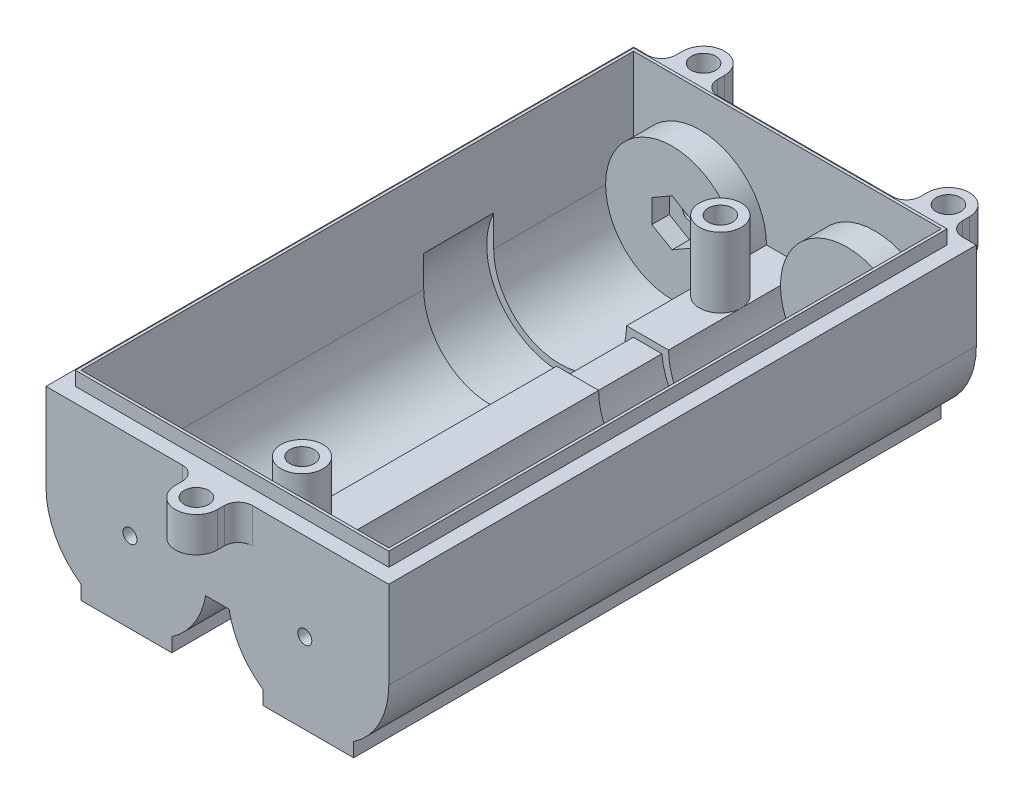
SolidWorks part; units mm, degrees
ref_plane "Спереди" through (0, 0, 0) normal (0, 0, 1) x (1, 0, 0)
ref_plane "Сверху" through (0, 0, 0) normal (0, 1, 0) x (1, 0, 0)
ref_plane "Справа" through (0, 0, 0) normal (1, 0, 0) x (0, 0, -1)
sketch "Эскиз1" plane through (0, 0, 0) normal (0, 1, 0) x (1, 0, 0)
  line L0 (-3, -45) -> (-3, -44)
  line L1 (22.5, 40) -> (-22.5, 40) construction
  line L2 (22.5, 40) -> (22.5, -40) construction
  line L3 (22.5, -40) -> (-22.5, -40) construction
  line L4 (-22.5, 40) -> (-22.5, -40) construction
  line L5 (22.5, 40) -> (-22.5, -40) construction
  line L6 (22.5, -40) -> (-22.5, 40) construction
  line L7 (22, -39.5) -> (-22, -39.5)
  line L8 (22, -39.5) -> (22, 39.5)
  line L9 (22, 39.5) -> (-22, 39.5)
  line L10 (-22, -39.5) -> (-22, 39.5)
  line L11 (22, -39.5) -> (-22, 39.5) construction
  line L12 (22, 39.5) -> (-22, -39.5) construction
  line L13 (24.5, -42) -> (5, -42)
  line L14 (24.5, -42) -> (24.5, 42)
  line L15 (24.5, 42) -> (22.5, 42)
  line L16 (-24.5, -42) -> (-24.5, 42)
  line L17 (24.5, -42) -> (-24.5, 42) construction
  line L18 (24.5, 42) -> (-24.5, -42) construction
  line L19 (-20.5, 45) -> (-20.5, 44)
  line L20 (3, -44) -> (3, -45)
  line L21 (-5, -42) -> (-24.5, -42)
  line L22 (-14.5, 45) -> (-14.5, 44)
  line L23 (14.5, 45) -> (14.5, 44)
  line L24 (20.5, 45) -> (20.5, 44)
  line L25 (12.5, 42) -> (-12.5, 42)
  line L26 (-22.5, 42) -> (-24.5, 42)
  circle A0 centre (-17.5, 45) radius 1.75
  circle A1 centre (17.5, 45) radius 1.75
  circle A2 centre (0, -45) radius 1.75
  arc A3 (-3, -45) -> (3, -45) centre (0, -45) ccw
  arc A4 (-14.5, 45) -> (-20.5, 45) centre (-17.5, 45) ccw
  arc A5 (20.5, 45) -> (14.5, 45) centre (17.5, 45) ccw
  arc A6 (5, -42) -> (3, -44) centre (5, -44) ccw
  arc A7 (-3, -44) -> (-5, -42) centre (-5, -44) ccw
  arc A8 (20.5, 44) -> (22.5, 42) centre (22.5, 44) ccw
  arc A9 (14.5, 44) -> (12.5, 42) centre (12.5, 44) cw
  arc A10 (-14.5, 44) -> (-12.5, 42) centre (-12.5, 44) ccw
  arc A11 (-20.5, 44) -> (-22.5, 42) centre (-22.5, 44) cw
  point P0 (0, 0)
  point P12 (0, -40)
  point P13 (0, 0)
  point P18 (0, 39.5)
  point P19 (-22, 0)
  point P20 (-22.5, 0)
  point P21 (0, 0)
  point P26 (-24.5, 0)
  point P27 (22, 0)
  point P44 (-3, -42)
  point P49 (14.5, 42)
  point P52 (-14.5, 42)
  point P55 (-20.5, 42)
  dimension "D3" = 3.5
  dimension "D4" = 3.5
  dimension "D5" = 5
  dimension "D9" = 3.5
  dimension "D16" = 6
  dimension "D17" = 6
  dimension "D18" = 6
  dimension "D19" = 2
  dimension "D1" = 45
  dimension "D2" = 80
  dimension "D6" = 5
  dimension "D7" = 5
  dimension "D8" = 5
  dimension "D10" = 5
  dimension "D11" = 0.5
  dimension "D12" = 0.5
  dimension "D13" = 2.5
  dimension "D14" = 2.5
  dimension "D15" = 2.5
extrude "Бобышка-Вытянуть1" add sketch "Эскиз1" along normal blind 5
sketch "Эскиз2" plane through (0, 0, 0) normal (0, -1, 0) x (1, 0, 0)
  line L1 (22, -39.5) -> (-22, -39.5)
  line L2 (22, -39.5) -> (22, 39.5)
  line L3 (22, 39.5) -> (-22, 39.5)
  line L4 (-22, -39.5) -> (-22, 39.5)
  line L5 (22, -39.5) -> (-22, 39.5) construction
  line L6 (22, 39.5) -> (-22, -39.5) construction
  line L7 (24.5, -42) -> (-24.5, -42)
  line L8 (24.5, -42) -> (24.5, 42)
  line L9 (24.5, 42) -> (-24.5, 42)
  line L10 (-24.5, -42) -> (-24.5, 42)
  line L11 (24.5, -42) -> (-24.5, 42) construction
  line L12 (24.5, 42) -> (-24.5, -42) construction
  point P0 (0, 0)
  point P7 (0, 0)
extrude "Бобышка-Вытянуть2" add sketch "Эскиз2" along normal blind 17
sketch "Эскиз3" plane through (0, 5, 0) normal (0, 1, 0) x (1, 0, 0)
  line L1 (22, -39.5) -> (-22, -39.5)
  line L2 (22, -39.5) -> (22, 39.5)
  line L3 (22, 39.5) -> (-22, 39.5)
  line L4 (-22, -39.5) -> (-22, 39.5)
  line L5 (22, -39.5) -> (-22, 39.5) construction
  line L6 (22, 39.5) -> (-22, -39.5) construction
  line L7 (-22.4, -39.9) -> (22.4, -39.9)
  line L8 (-22.4, -39.9) -> (-22.4, 39.9)
  line L9 (-22.4, 39.9) -> (22.4, 39.9)
  line L10 (22.4, -39.9) -> (22.4, 39.9)
  line L11 (-22.4, -39.9) -> (22.4, 39.9) construction
  line L12 (-22.4, 39.9) -> (22.4, -39.9) construction
  point P0 (0, 0)
  point P7 (0, 0)
  point P12 (0, 39.5)
  point P13 (0, 39.9)
  point P14 (22, 0)
  dimension "D1" = 0.4
  dimension "D2" = 0.4
extrude "Бобышка-Вытянуть3" add sketch "Эскиз3" along normal blind 2
sketch "Эскиз4" plane through (0, -17, 0) normal (0, -1, 0) x (1, 0, 0)
  line L1 (24.5, -42) -> (-24.5, -42)
  line L2 (24.5, -42) -> (24.5, 42)
  line L3 (24.5, 42) -> (-24.5, 42)
  line L4 (-24.5, -42) -> (-24.5, 42)
  line L5 (24.5, -42) -> (-24.5, 42) construction
  line L6 (24.5, 42) -> (-24.5, -42) construction
  point P0 (0, 0)
extrude "Бобышка-Вытянуть4" add sketch "Эскиз4" along normal blind 2
sketch "Эскиз5" plane through (0, 0, -39.5) normal (0, 0, 1) x (1, 0, 0)
  line L0 (-22, 7) -> (-22, -17) construction
  line L1 (-22, -17) -> (22, -17) construction
  line L2 (22, 7) -> (22, -17) construction
  line L3 (-3, -7.5) -> (3, -7.5)
  line L4 (-22, -7.5) -> (-22, -17)
  line L5 (-22, -17) -> (22, -17)
  line L6 (22, -17) -> (22, -7.5)
  arc A0 (-22, -7.5) -> (-3, -7.5) centre (-12.5, -7.5) ccw
  arc A1 (3, -7.5) -> (22, -7.5) centre (12.5, -7.5) ccw
  line M1 (-22, 7) -> (-22, -17)
  line M2 (-22, -17) -> (22, -17)
  line M3 (22, -17) -> (22, 7)
  dimension "D1" = 19
  dimension "D2" = 19
extrude "Бобышка-Вытянуть5" add sketch "Эскиз5" along normal up to surface (79 mm away) contours A1 L3 A0 L5 | A0 M1 M2 | A1 M2 M3 up to face at (0, -5, 39.5)
sketch "Эскиз6" plane through (0, 0, -39.5) normal (0, 0, 1) x (1, 0, 0)
  line L0 (-2.0425, -8.4439) -> (2.0425, -8.4439)
  line L1 (-3, -7.5) -> (3, -7.5) construction
  line L2 (-12.5, 3) -> (12.5, 3)
  arc A0 (-12.5, 3) -> (-2.0425, -8.4439) centre (-12.5, -7.5) ccw
  arc A1 (2.0425, -8.4439) -> (12.5, 3) centre (12.5, -7.5) ccw
  point P8 (0, -8.4439)
  point P11 (0, -7.5)
  dimension "D1" = 21
  dimension "D2" = 21
  dimension "D3" = 0.9439
extrude "Вырез-Вытянуть1" cut sketch "Эскиз6" along normal blind 10 from offset 20
sketch "Эскиз7" plane through (0, -7.5, 0) normal (0, 1, 0) x (1, 0, 0)
  line L0 (-22.4, -39.9) -> (22.4, -39.9) construction
  line L1 (22.4, 39.9) -> (-22.4, 39.9) construction
  circle A0 centre (0, 29.9) radius 1.75
  circle A1 centre (0, -29.9) radius 1.75
  point P6 (0, -39.9)
  point P9 (0, 39.9)
  dimension "D2" = 3.5
  dimension "D3" = 3.5
  dimension "D1" = 10
  dimension "D4" = 10
extrude "Вырез-Вытянуть2" cut sketch "Эскиз7" against normal through all
sketch "Эскиз8" plane through (0, 0, 42) normal (0, 0, 1) x (1, 0, 0)
  line L0 (-24.5, -17) -> (24.5, -17) construction
  line L1 (-24.5, 5) -> (-24.5, -19) construction
  line L2 (24.5, 5) -> (24.5, -19) construction
  line L3 (24.5, -19) -> (-24.5, -19) construction
  line L4 (-1.6752, -9.5) -> (1.6752, -9.5)
  line L5 (-13, -7.5) -> (13, -7.5) construction
  line L6 (-6.5193, -19) -> (6.5193, -19)
  line L7 (19.4807, -19) -> (24.5, -19)
  line L8 (24.5, -19) -> (24.5, -7.5)
  line L9 (-24.5, -7.5) -> (-24.5, -19)
  line L10 (-24.5, -19) -> (-19.4807, -19)
  line L11 (-19.4807, -17) -> (-19.4807, -19)
  line L12 (-6.5193, -17) -> (-6.5193, -19)
  line L13 (6.5193, -17) -> (6.5193, -19)
  line L14 (19.4807, -17) -> (19.4807, -19)
  arc A0 (19.4807, -17) -> (24.5, -7.5) centre (13, -7.5) ccw
  arc A1 (-6.5193, -17) -> (-1.6752, -9.5) centre (-13, -7.5) ccw
  arc A2 (-24.5, -7.5) -> (-19.4807, -17) centre (-13, -7.5) ccw
  arc A3 (1.6752, -9.5) -> (6.5193, -17) centre (13, -7.5) ccw
  point P10 (0, -17)
  point P17 (0, -7.5)
  point P18 (0, -9.5)
  dimension "D8" = 23
  dimension "D3" = 2
  dimension "D7" = 11.5
  dimension "D9" = 2
extrude "Вырез-Вытянуть3" cut sketch "Эскиз8" against normal through all
sketch "Эскиз9" plane through (0, -7.5, 0) normal (0, 1, 0) x (1, 0, 0)
  circle A0 centre (0, 29.9) radius 1.75
  circle A1 centre (0, 29.9) radius 3
  circle A2 centre (0, -29.9) radius 1.75
  circle A3 centre (0, -29.9) radius 3
extrude "Бобышка-Вытянуть6" add sketch "Эскиз9" along normal blind 10
sketch "Эскиз11" plane through (0, -9.5, 0) normal (0, -1, 0) x (1, 0, 0)
  line L1 (-3, -24.9) -> (3, -24.9)
  line L2 (-3, -24.9) -> (-3, -34.9)
  line L3 (-3, -34.9) -> (3, -34.9)
  line L4 (3, -24.9) -> (3, -34.9)
  line L5 (-3, -24.9) -> (3, -34.9) construction
  line L6 (-3, -34.9) -> (3, -24.9) construction
  line L7 (-3, 34.9) -> (3, 34.9)
  line L8 (-3, 34.9) -> (-3, 24.9)
  line L9 (-3, 24.9) -> (3, 24.9)
  line L10 (3, 34.9) -> (3, 24.9)
  line L11 (-3, 34.9) -> (3, 24.9) construction
  line L12 (-3, 24.9) -> (3, 34.9) construction
  circle A0 centre (0, 29.9) radius 1.75
  circle A1 centre (0, -29.9) radius 1.75
  dimension "D1" = 6
  dimension "D2" = 10
  dimension "D3" = 10
  dimension "D4" = 6
extrude "Бобышка-Вытянуть7" add sketch "Эскиз11" along normal blind 3.5
sketch "Эскиз12" plane through (0, -13, 0) normal (0, -1, 0) x (1, 0, 0)
  line L1 (0, 26.5745) -> (2.88, 28.2372)
  line L2 (2.88, 28.2372) -> (2.88, 31.5628)
  line L3 (2.88, 31.5628) -> (0, 33.2255)
  line L4 (0, 33.2255) -> (-2.88, 31.5628)
  line L5 (-2.88, 31.5628) -> (-2.88, 28.2372)
  line L6 (-2.88, 28.2372) -> (0, 26.5745)
  line L7 (0, -33.2255) -> (2.88, -31.5628)
  line L8 (2.88, -31.5628) -> (2.88, -28.2372)
  line L9 (2.88, -28.2372) -> (0, -26.5745)
  line L10 (0, -26.5745) -> (-2.88, -28.2372)
  line L11 (-2.88, -28.2372) -> (-2.88, -31.5628)
  line L12 (-2.88, -31.5628) -> (0, -33.2255)
  circle A0 centre (0, 29.9) radius 2.88 construction
  circle A1 centre (0, -29.9) radius 2.88 construction
  dimension "D1" = 5.76
  dimension "D2" = 5.76
extrude "Вырез-Вытянуть4" cut sketch "Эскиз12" against normal blind 3.5
sketch "Эскиз13" plane through (0, 0, -39.5) normal (0, 0, 1) x (1, 0, 0)
  circle A0 centre (-12.5, -7.5) radius 9.5
  circle A1 centre (12.5, -7.5) radius 9.5
extrude "Бобышка-Вытянуть8" add sketch "Эскиз13" along normal blind 4
sketch "Эскиз14" plane through (0, 0, 39.5) normal (0, 0, -1) x (-1, 0, 0)
  circle A0 centre (-12.5, -7.5) radius 9.5
  circle A1 centre (12.5, -7.5) radius 9.5
extrude "Бобышка-Вытянуть9" add sketch "Эскиз14" along normal blind 4
sketch "Эскиз15" plane through (0, 0, -35.5) normal (0, 0, 1) x (1, 0, 0)
  line L1 (-12.5, -10.8486) -> (-9.6, -9.1743)
  line L2 (-9.6, -9.1743) -> (-9.6, -5.8257)
  line L3 (-9.6, -5.8257) -> (-12.5, -4.1514)
  line L4 (-12.5, -4.1514) -> (-15.4, -5.8257)
  line L5 (-15.4, -5.8257) -> (-15.4, -9.1743)
  line L6 (-15.4, -9.1743) -> (-12.5, -10.8486)
  line L7 (12.5, -10.8486) -> (15.4, -9.1743)
  line L8 (15.4, -9.1743) -> (15.4, -5.8257)
  line L9 (15.4, -5.8257) -> (12.5, -4.1514)
  line L10 (12.5, -4.1514) -> (9.6, -5.8257)
  line L11 (9.6, -5.8257) -> (9.6, -9.1743)
  line L12 (9.6, -9.1743) -> (12.5, -10.8486)
  circle A0 centre (-12.5, -7.5) radius 2.9 construction
  circle A1 centre (12.5, -7.5) radius 2.9 construction
  dimension "D1" = 5.8
  dimension "D2" = 5.8
extrude "Вырез-Вытянуть5" cut sketch "Эскиз15" against normal blind 2.5
sketch "Эскиз16" plane through (0, 0, -38) normal (0, 0, 1) x (1, 0, 0)
  circle A0 centre (12.5, -7.5) radius 1
  circle A1 centre (-12.5, -7.5) radius 1
  dimension "D1" = 2
  dimension "D2" = 2
extrude "Вырез-Вытянуть6" cut sketch "Эскиз16" against normal through all
sketch "Эскиз17" plane through (0, 0, 35.5) normal (0, 0, -1) x (-1, 0, 0)
  circle A0 centre (-12.5, -7.5) radius 3.75
  circle A1 centre (12.5, -7.5) radius 3.75
  dimension "D1" = 7.5
  dimension "D2" = 7.5
extrude "Вырез-Вытянуть7" cut sketch "Эскиз17" against normal blind 3
sketch "Эскиз18" plane through (0, 0, 38.5) normal (0, 0, -1) x (-1, 0, 0)
  circle A0 centre (-12.5, -7.5) radius 1
  circle A1 centre (12.5, -7.5) radius 1
  dimension "D1" = 2
  dimension "D2" = 2
extrude "Вырез-Вытянуть8" cut sketch "Эскиз18" against normal through all
